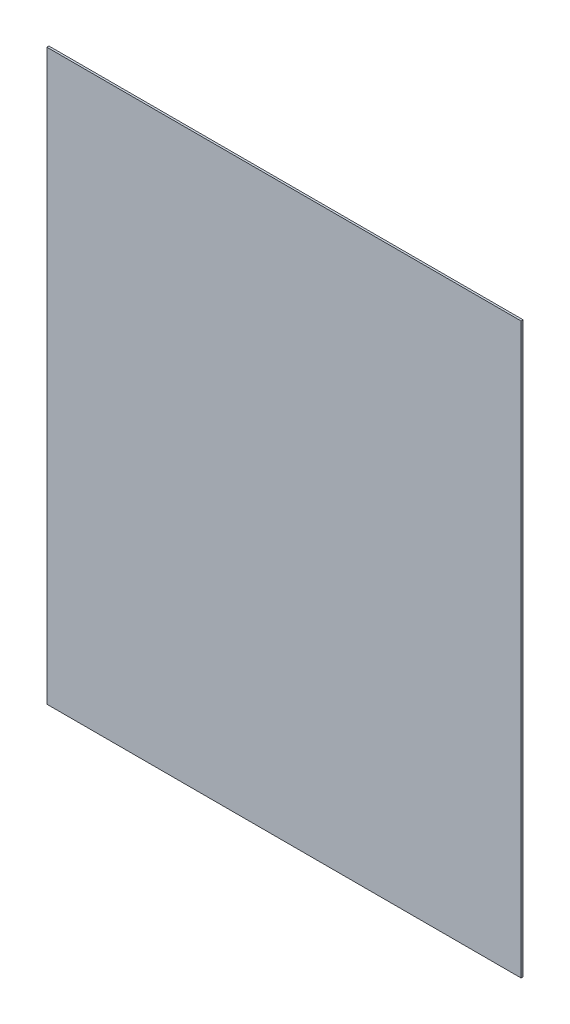
SolidWorks part; units mm, degrees
ref_plane "Front Plane" through (0, 0, 0) normal (0, 0, 1) x (1, 0, 0)
ref_plane "Top Plane" through (0, 0, 0) normal (0, 1, 0) x (1, 0, 0)
ref_plane "Right Plane" through (0, 0, 0) normal (1, 0, 0) x (0, 0, -1)
sketch "Sketch1" plane through (0, 0, 0) normal (0, 0, 1) x (1, 0, 0)
  line L0 (-798.576, 865.124) -> (-14.224, 865.124) construction
  line L1 (-26.924, 865.124) -> (-788.924, 865.124)
  line L2 (-26.924, 865.124) -> (-26.924, 1779.524)
  line L3 (-26.924, 1779.524) -> (-788.924, 1779.524)
  line L4 (-788.924, 865.124) -> (-788.924, 1779.524)
  line L5 (-14.224, 0) -> (-14.224, 865.124) construction
  dimension "D1" = 762
  dimension "D2" = 914.4
  dimension "D3" = 12.7
extrude "Boss-Extrude1" add sketch "Sketch1" against normal blind 3.302
